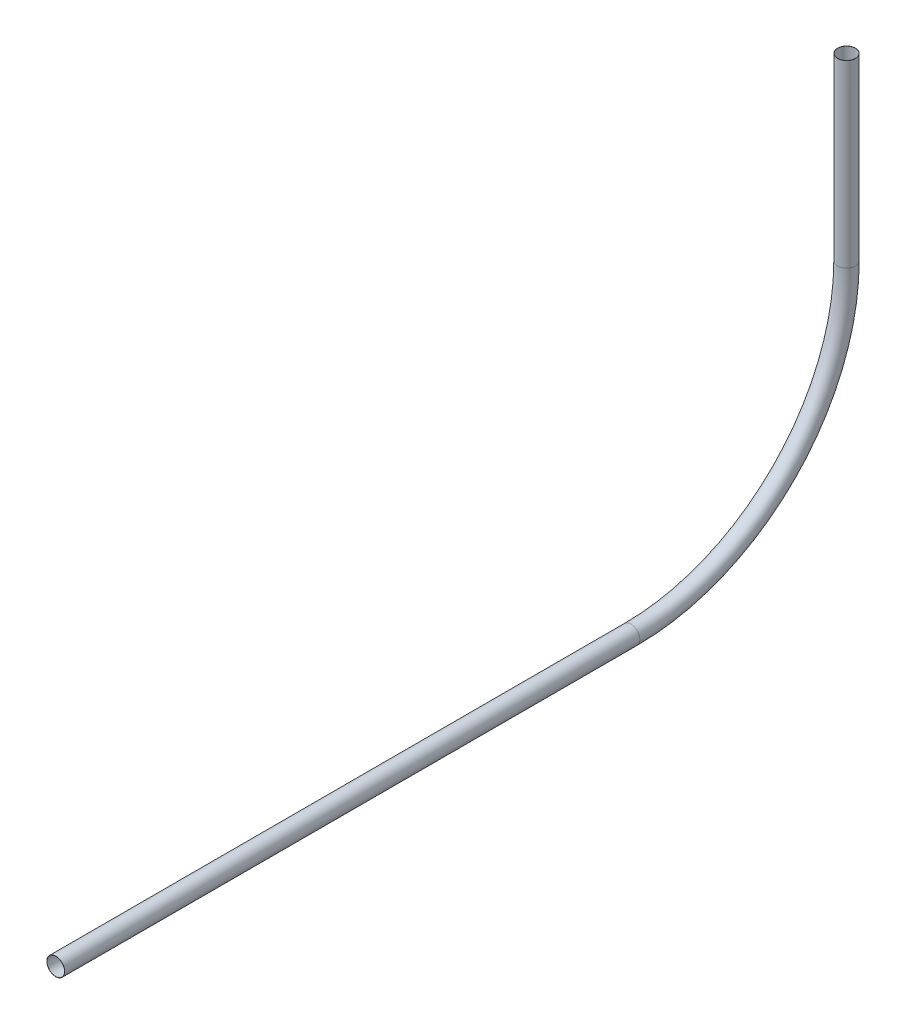
SolidWorks part; units mm, degrees
ref_plane "Front Plane" through (0, 0, 0) normal (0, 0, 1) x (1, 0, 0)
ref_plane "Top Plane" through (0, 0, 0) normal (0, 1, 0) x (1, 0, 0)
ref_plane "Right Plane" through (0, 0, 0) normal (1, 0, 0) x (0, 0, -1)
sketch "Sketch1" plane through (0, 0, 0) normal (0, 1, 0) x (1, 0, 0)
  circle A0 centre (0, 0) radius 1.5875
  circle A1 centre (0, 0) radius 1.5494
  dimension "D1" = 3.175
  dimension "D2" = 3.0988
sketch "Sketch2" plane through (0, 0, 0) normal (1, 0, 0) x (0, 0, -1)
  line L0 (0, 0) -> (0, -31.75)
  line L1 (-38.1, -69.85) -> (-139.7, -69.85)
  arc A0 (0, -31.75) -> (-38.1, -69.85) centre (-38.1, -31.75) cw
  dimension "D3" = 38.1
  dimension "D1" = 31.75
  dimension "D2" = 101.6
sweep "Sweep1" add profiles "Sketch1" path "Sketch2"
